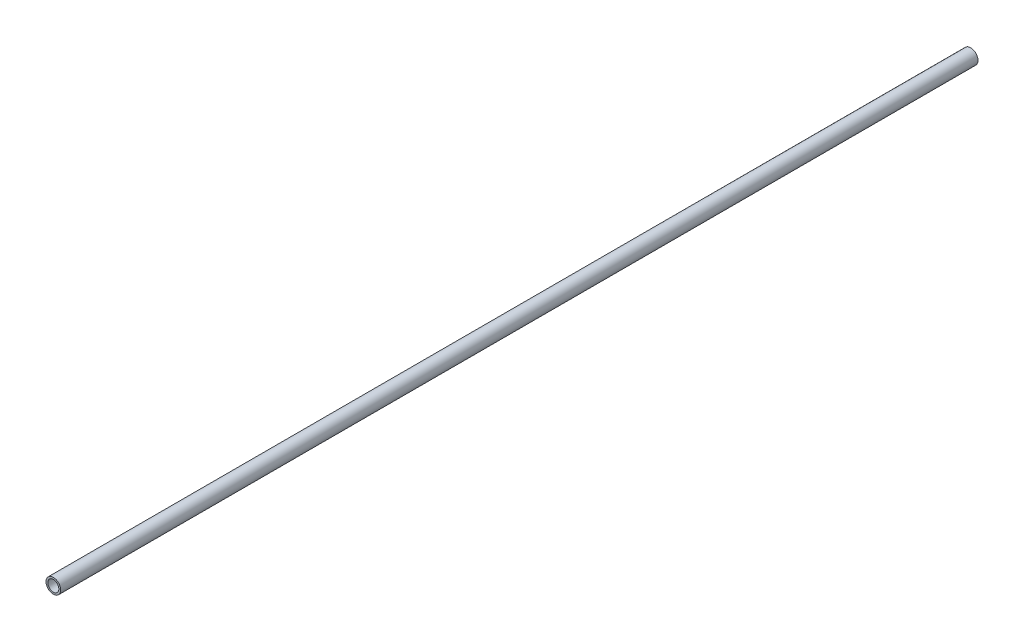
SolidWorks part; units mm, degrees
ref_plane "Front Plane" through (0, 0, 0) normal (0, 0, 1) x (1, 0, 0)
ref_plane "Top Plane" through (0, 0, 0) normal (0, 1, 0) x (1, 0, 0)
ref_plane "Right Plane" through (0, 0, 0) normal (1, 0, 0) x (0, 0, -1)
sketch "Sketch1" plane through (0, 0, 0) normal (0, 0, 1) x (1, 0, 0)
  circle A0 centre (0, 0) radius 2
  circle A1 centre (0, 0) radius 1.5
  dimension "D1" = 4
  dimension "D2" = 3
extrude "Boss-Extrude1" add sketch "Sketch1" along normal blind 250
